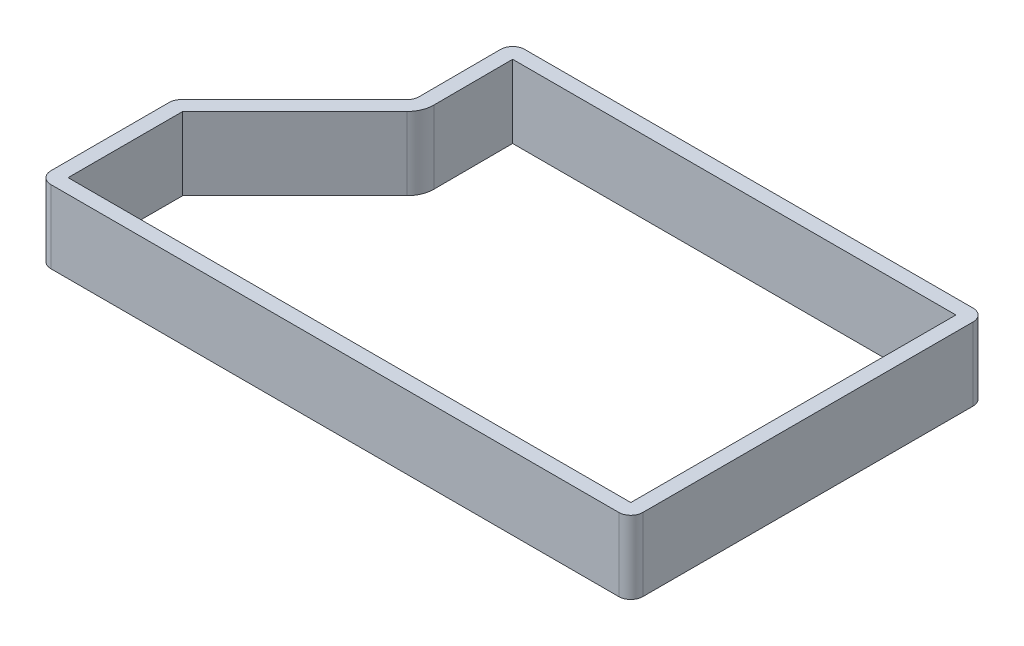
SolidWorks part; units mm, degrees
ref_plane "Front Plane" through (0, 0, 0) normal (0, 0, 1) x (1, 0, 0)
ref_plane "Top Plane" through (0, 0, 0) normal (0, 1, 0) x (1, 0, 0)
ref_plane "Right Plane" through (0, 0, 0) normal (1, 0, 0) x (0, 0, -1)
sketch "Sketch1" plane through (0, 0, 0) normal (0, 1, 0) x (1, 0, 0)
  line L16 (-46.4052, -22.2394) -> (31.4342, -22.2393)
  line L17 (33.0842, -20.59) -> (33.1033, 24.6566)
  line L18 (31.4526, 26.3073) -> (-29.9917, 26.2822)
  line L19 (-31.6396, 24.7021) -> (-31.6021, 13.4439)
  line L20 (-32.0854, 12.2716) -> (-47.5719, -3.2149)
  line L21 (-48.0552, -4.3817) -> (-48.0552, -20.5894)
  arc A12 (-48.0552, -20.5894) -> (-46.4052, -22.2394) centre (-46.4052, -20.5894) ccw
  arc A13 (31.4342, -22.2393) -> (33.0842, -20.59) centre (31.4342, -20.5893) ccw
  arc A14 (33.1033, 24.6566) -> (31.4526, 26.3073) centre (31.4533, 24.6573) ccw
  arc A15 (-29.9917, 26.2822) -> (-31.6396, 24.7021) centre (-29.9911, 24.6322) ccw
  arc A16 (-32.0854, 12.2716) -> (-31.6021, 13.4439) centre (-33.2521, 13.4384) ccw
  arc A17 (-47.5719, -3.2149) -> (-48.0552, -4.3817) centre (-46.4052, -4.3817) ccw
extrude "Extrude-Thin1" add sketch "Sketch1" along normal blind 10 thin
